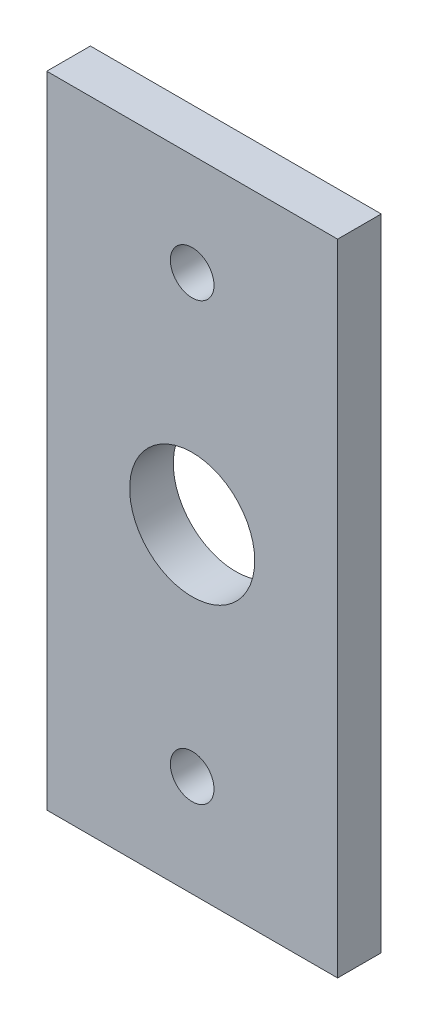
SolidWorks part; units mm, degrees
ref_plane "Front Plane" through (0, 0, 0) normal (0, 0, 1) x (1, 0, 0)
ref_plane "Top Plane" through (0, 0, 0) normal (0, 1, 0) x (1, 0, 0)
ref_plane "Right Plane" through (0, 0, 0) normal (1, 0, 0) x (0, 0, -1)
sketch "Sketch1" plane through (0, 0, 0) normal (0, 0, 1) x (1, 0, 0)
  line L0 (10, 0) -> (10, -44) construction
  line L1 (0, 0) -> (20, 0)
  line L2 (0, 0) -> (0, -44)
  line L3 (0, -44) -> (20, -44)
  line L4 (20, 0) -> (20, -44)
  circle A0 centre (10, -7) radius 1.5
  circle A1 centre (10, -37) radius 1.5
  circle A2 centre (10, -22) radius 4.3
  dimension "D3" = 3
  dimension "D4" = 3
  dimension "D7" = 8.6
  dimension "D1" = 44
  dimension "D2" = 20
  dimension "D5" = 7
  dimension "D6" = 7
extrude "Boss-Extrude1" add sketch "Sketch1" along normal blind 3
